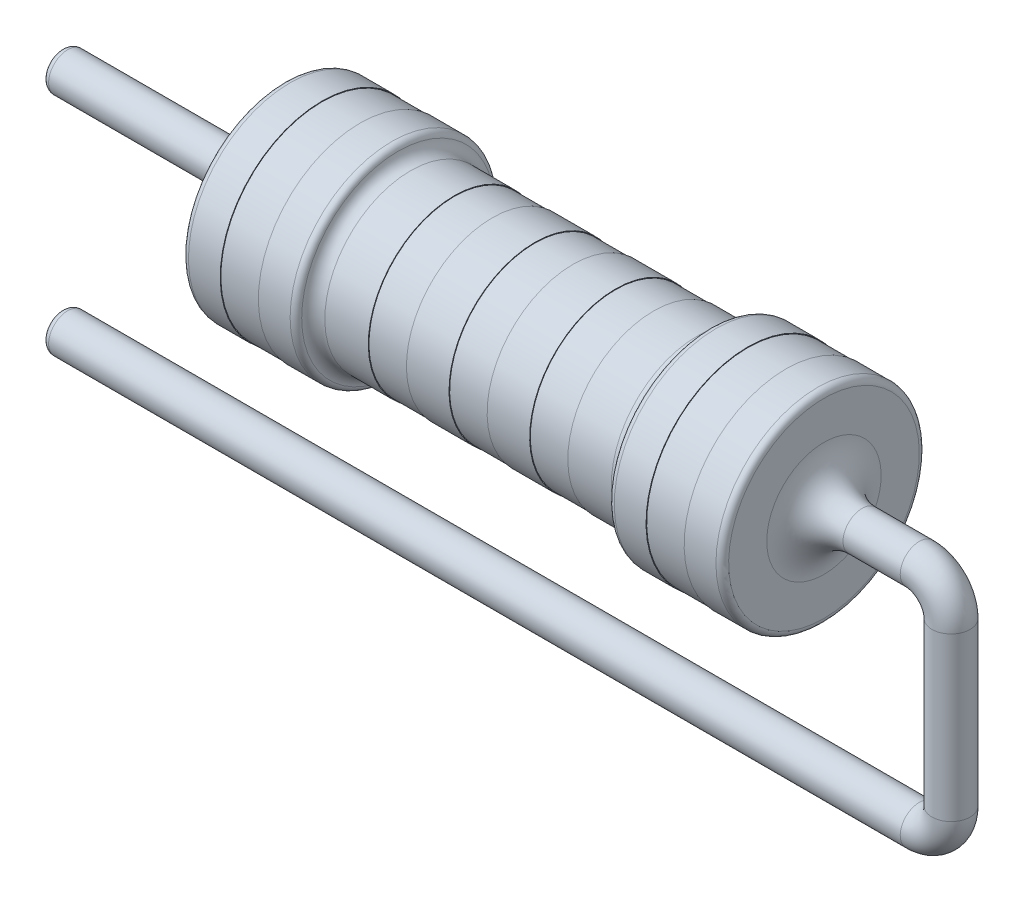
SolidWorks part; units mm, degrees
ref_plane "Front Plane" through (0, 0, 0) normal (0, 0, 1) x (1, 0, 0)
ref_plane "Top Plane" through (0, 0, 0) normal (0, 1, 0) x (1, 0, 0)
ref_plane "Right Plane" through (0, 0, 0) normal (1, 0, 0) x (0, 0, -1)
sketch "Sketch1" plane through (0, 0, 0) normal (0, 0, 1) x (1, 0, 0)
  line L0 (4.25, 0) -> (-4.25, 0)
  line L1 (4.25, 0) -> (4.25, -1.6)
  line L2 (4.25, -1.6) -> (3.65, -1.6)
  line L3 (3.65, -1.6) -> (3.65, -1.59)
  line L4 (3.65, -1.59) -> (3.05, -1.59)
  line L5 (3.05, -1.59) -> (3.05, -1.6)
  line L6 (3.05, -1.6) -> (2.45, -1.6)
  line L7 (2.45, -1.6) -> (2.45, -1.35)
  line L8 (2.45, -1.35) -> (1.5695, -1.35)
  line L9 (1.5695, -1.35) -> (1.5695, -1.34)
  line L10 (1.5695, -1.34) -> (0.9695, -1.34)
  line L11 (0.9695, -1.34) -> (0.9695, -1.35)
  line L12 (0.9695, -1.35) -> (0.3, -1.35)
  line L14 (-0.3, -1.34) -> (-0.3, -1.35)
  line L15 (-0.3, -1.34) -> (0.3, -1.34)
  line L16 (0.3, -1.34) -> (0.3, -1.35)
  line L17 (-0.9695, -1.35) -> (-0.3, -1.35)
  line L18 (-0.9695, -1.34) -> (-0.9695, -1.35)
  line L19 (-1.5695, -1.34) -> (-0.9695, -1.34)
  line L20 (-1.5695, -1.35) -> (-1.5695, -1.34)
  line L21 (-2.45, -1.35) -> (-1.5695, -1.35)
  line L22 (-2.45, -1.6) -> (-2.45, -1.35)
  line L23 (-3.05, -1.6) -> (-2.45, -1.6)
  line L24 (-3.05, -1.59) -> (-3.05, -1.6)
  line L25 (-3.65, -1.59) -> (-3.05, -1.59)
  line L26 (-3.65, -1.6) -> (-3.65, -1.59)
  line L27 (-4.25, -1.6) -> (-3.65, -1.6)
  line L28 (-4.25, 0) -> (-4.25, -1.6)
  dimension "D2" = 1.6
  dimension "D3" = 1.8
  dimension "D4" = 0.6
  dimension "D5" = 0.6
  dimension "D6" = 0.6
  dimension "D8" = 0.01
  dimension "D9" = 0.25
  dimension "D10" = 0.01
  dimension "D11" = 0.01
revolve "Revolve2" add sketch "Sketch1" angle 360 about L0
sketch "Sketch3" plane through (4.25, 0, 0) normal (1, 0, 0) x (0, 0, -1)
  circle A0 centre (0, 0) radius 0.3
sketch3d "3DSketch3"
  line L0 (4.25, 0, 0) -> (5.75, 0, 0)
  line L1 (6.25, -0.5, 0) -> (6.25, -3.0567, 0)
  line L2 (5.75, -3.5567, 0) -> (-7.75, -3.5567, 0)
  arc A0 (6.25, -0.5, 0) -> (5.75, 0, 0) centre (5.75, -0.5, 0) ccw
  arc A1 (5.75, -3.5567, 0) -> (6.25, -3.0567, 0) centre (5.75, -3.0567, 0) ccw
  point P6 (6.25, 0, 0)
  point P7 (5.75, -0.5, 0.5)
  point P11 (6.25, -3.5567, 0)
  point P12 (5.75, -3.0567, 0.5)
  dimension "D2" = 0.5
  dimension "D4" = 0.5
  dimension "D1" = 2
  dimension "D3" = 14
fillet "Fillet10" radius 0.1 4 edges at (2.45, 1.6, 0) (-2.45, 1.6, 0) (4.25, 1.6, 0) (-4.25, 1.6, 0)
fillet "Fillet11" radius 0.2 2 edges at (2.45, 1.35, 0) (-2.45, 1.35, 0)
sketch3d "3DSketch4" plane through (0, 0, 0) normal (0, 0, 1) x (1, 0, 0)
sweep "Sweep1" add profiles "Sketch3" path "3DSketch3"
sketch "Sketch4" plane through (-4.25, 0, 0) normal (-1, 0, 0) x (0, 0, 1)
  circle A0 centre (0, 0) radius 0.3
sketch3d "3DSketch6"
  line L0 (-4.25, 0, 0) -> (-7.75, 0, 0)
  dimension "D1" = 3.5
sweep "Sweep2" add profiles "Sketch4" path "3DSketch6"
fillet "Fillet12" radius 0.1 2 edges at (-7.75, -0.3, 0) (-7.75, -3.8567, 0)
fillet "Fillet13" radius 0.6 2 edges at (-4.25, -0.3, 0) (4.25, 0.3, 0)
